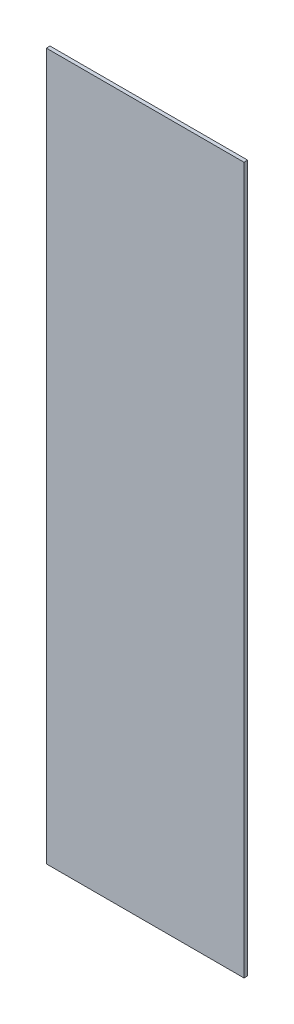
SolidWorks part; units mm, degrees
material "PE High Density"
ref_plane "Front Plane" through (0, 0, 0) normal (0, 0, 1) x (1, 0, 0)
ref_plane "Top Plane" through (0, 0, 0) normal (0, 1, 0) x (1, 0, 0)
ref_plane "Right Plane" through (0, 0, 0) normal (1, 0, 0) x (0, 0, -1)
sketch "Sketch1" plane through (0, 0, 0) normal (0, 1, 0) x (1, 0, 0)
  line L1 (0, 0) -> (171.45, 0)
  line L2 (0, 0) -> (0, 3.175)
  line L3 (0, 3.175) -> (171.45, 3.175)
  line L4 (171.45, 0) -> (171.45, 3.175)
  dimension "D1" = 171.45
  dimension "D2" = 3.175
extrude "Boss-Extrude1" add sketch "Sketch1" along normal mid plane 612.775
